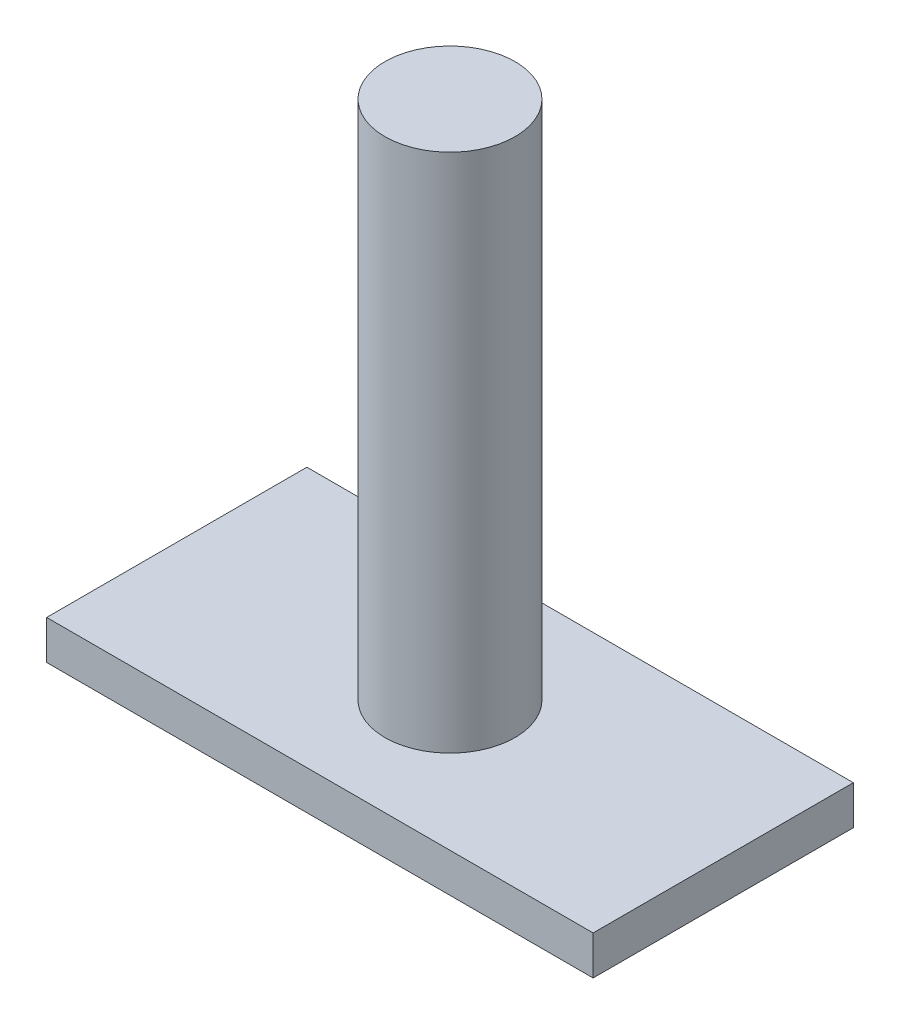
SolidWorks part; units mm, degrees
ref_plane "Front Plane" through (0, 0, 0) normal (0, 0, 1) x (1, 0, 0)
ref_plane "Top Plane" through (0, 0, 0) normal (0, 1, 0) x (1, 0, 0)
ref_plane "Right Plane" through (0, 0, 0) normal (1, 0, 0) x (0, 0, -1)
sketch "Sketch1" plane through (0, 0, 0) normal (0, 1, 0) x (1, 0, 0)
  line L1 (0, 0) -> (53.34, 0)
  line L2 (0, 0) -> (0, 25.4)
  line L3 (0, 25.4) -> (53.34, 25.4)
  line L4 (53.34, 0) -> (53.34, 25.4)
  dimension "D1" = 25.4
  dimension "D2" = 53.34
extrude "Boss-Extrude1" add sketch "Sketch1" along normal blind 3.81
sketch "Sketch2" plane through (0, 3.81, 0) normal (0, 1, 0) x (1, 0, 0)
  circle A0 centre (26.67, 12.7) radius 6.35
  dimension "D1" = 12.7
extrude "Boss-Extrude2" add sketch "Sketch2" along normal blind 50.8
